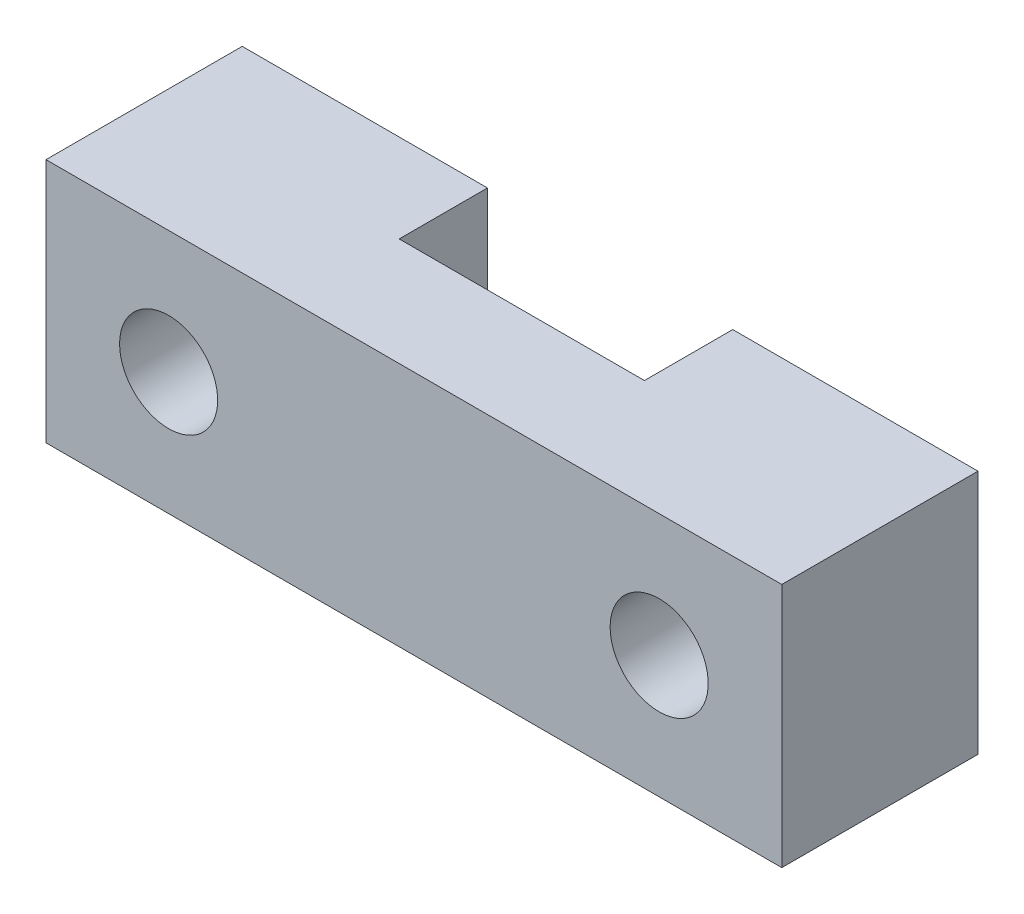
SolidWorks part; units mm, degrees
ref_plane "Plan de face" through (0, 0, 0) normal (0, 0, 1) x (1, 0, 0)
ref_plane "Plan de dessus" through (0, 0, 0) normal (0, 1, 0) x (1, 0, 0)
ref_plane "Plan de droite" through (0, 0, 0) normal (1, 0, 0) x (0, 0, -1)
sketch "Esquisse1" plane through (0, 0, 0) normal (0, 1, 0) x (1, 0, 0)
  line L1 (7.5, 2) -> (-7.5, 2)
  line L2 (7.5, 2) -> (7.5, -2)
  line L3 (7.5, -2) -> (-7.5, -2)
  line L4 (-7.5, 2) -> (-7.5, -2)
  line L5 (7.5, 2) -> (-7.5, -2) construction
  line L6 (7.5, -2) -> (-7.5, 2) construction
  point P0 (0, 0)
  dimension "D1" = 4
  dimension "D2" = 15
extrude "Boss.-Extru.1" add sketch "Esquisse1" along normal blind 5
sketch "Esquisse2" plane through (0, 5, 0) normal (0, 1, 0) x (1, 0, 0)
  line L0 (7.5, 2) -> (-7.5, 2) construction
  line L1 (-2.5, 2) -> (2.5, 2)
  line L2 (-2.5, 2) -> (-2.5, 0.2)
  line L3 (-2.5, 0.2) -> (2.5, 0.2)
  line L4 (2.5, 2) -> (2.5, 0.2)
  line L5 (0, -2) -> (0, 0.2) construction
  line L6 (-7.5, -2) -> (7.5, -2) construction
  dimension "D1" = 5
  dimension "D2" = 1.8
extrude "Enlèv. mat.-Extru.1" cut sketch "Esquisse2" against normal blind 5
sketch "Esquisse3" plane through (0, 0, -2) normal (0, 0, -1) x (-1, 0, 0)
  line L0 (0, 0) -> (0, 5) construction
  line L1 (2.5, 5) -> (-2.5, 5) construction
  circle A0 centre (5, 2.5) radius 1
  circle A1 centre (-5, 2.5) radius 1
  dimension "D1" = 2
extrude "Enlèv. mat.-Extru.2" cut sketch "Esquisse3" against normal blind 5
